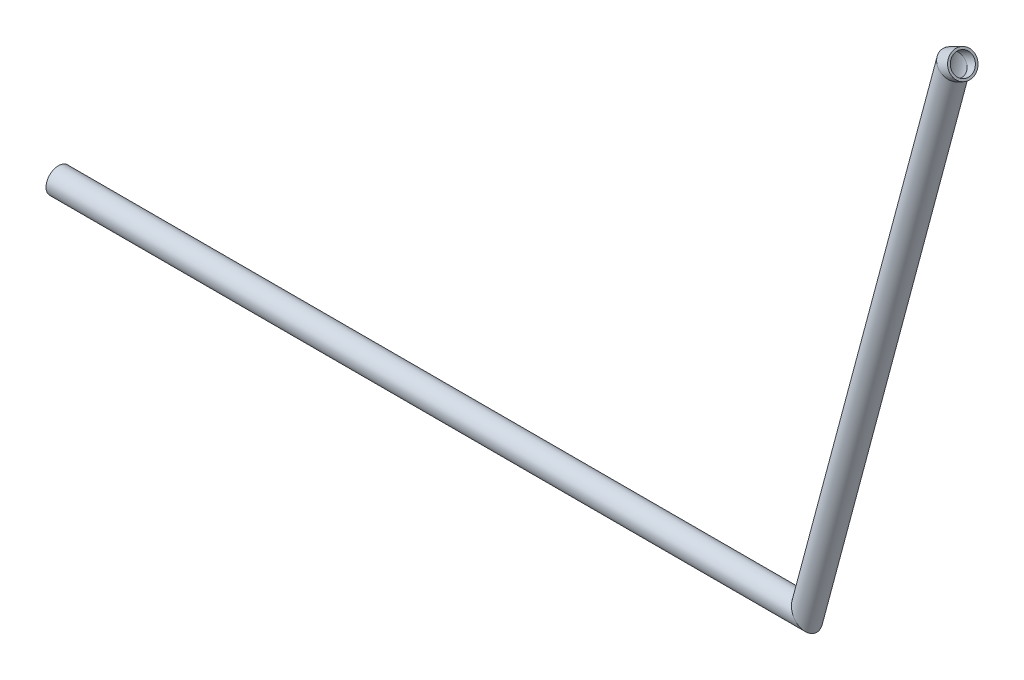
SolidWorks part; units mm, degrees
ref_plane "Front Plane" through (0, 0, 0) normal (0, 0, 1) x (1, 0, 0)
ref_plane "Top Plane" through (0, 0, 0) normal (0, 1, 0) x (1, 0, 0)
ref_plane "Right Plane" through (0, 0, 0) normal (1, 0, 0) x (0, 0, -1)
sketch3d "3DSketch1"
  line L0 (715.6766, 365.261, 100.9471) -> (707.1451, 360.2086, 99.6481)
  line L1 (707.1451, 360.2086, 99.6481) -> (595.9, -56.7274, 99.6481)
  line L2 (595.9, -56.7274, 99.6481) -> (25.9, -56.7274, 99.6481)
  line L3 (712.8329, 369.3871, 109.4205) -> (717.6454, 372.237, 110.1532) construction
  line L4 (595.9, -56.7274, 99.6481) -> (707.1451, -56.7274, 99.6481) construction
  line L5 (707.1451, -56.7274, 99.6481) -> (707.1451, 360.2086, 99.6481) construction
  point P2 (0, 0, 0)
  point P3 (0, 0, 0)
  point P4 (0, 0, 0)
  point P5 (0, 0, 0)
  dimension "D3" = 10
  dimension "D4" = 570
  dimension "D1" = 416.936
  dimension "D2" = 111.2451
other "Al round tubing AL RND TUBE 0.75 OD X 0.065 WALL(1)"
ref_plane "Plane1" through (595.9, -56.7274, 99.6481) normal (-1, 0, 0) x (0, 0, 1)
sketch "Sketch1" plane through (595.9, -56.7274, 99.6481) normal (-1, 0, 0) x (0, 0, 1)
  circle A0 centre (0, 0) radius 7.874
  circle A1 centre (0, 0) radius 9.525
  point P3 (0, 0)
  dimension "In_dia" = 15.748
  dimension "Out_dia" = 19.05
